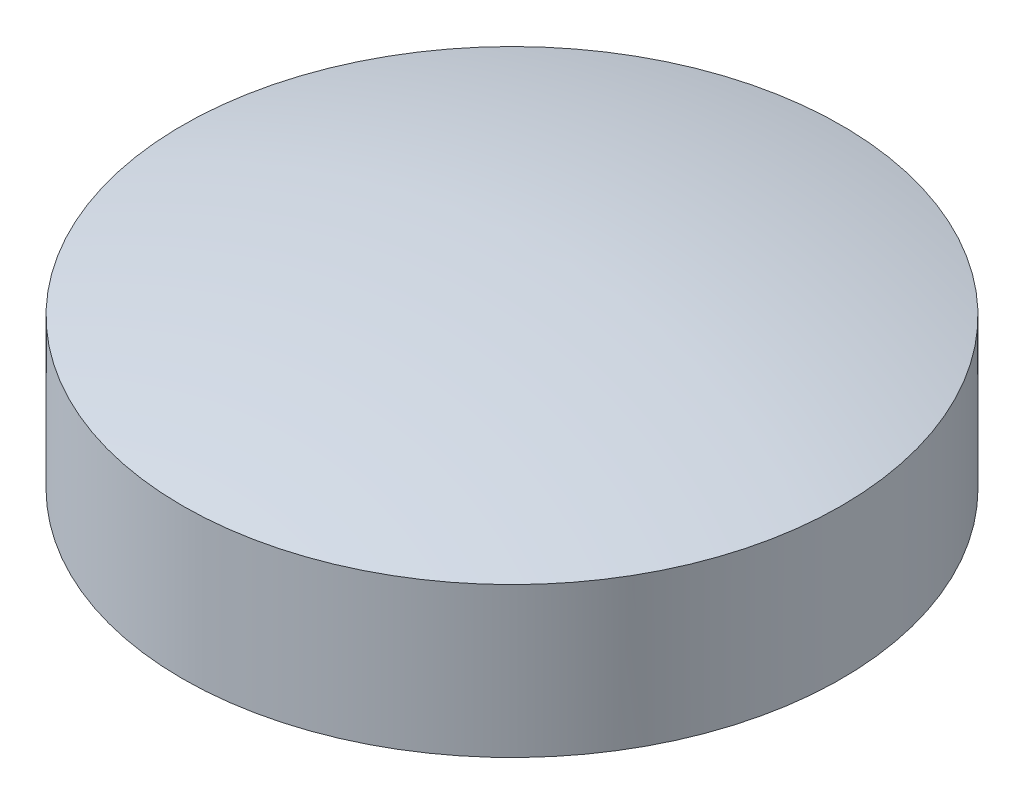
SolidWorks part; units mm, degrees
ref_plane "Front Plane" through (0, 0, 0) normal (0, 0, 1) x (1, 0, 0)
ref_plane "Top Plane" through (0, 0, 0) normal (0, 1, 0) x (1, 0, 0)
ref_plane "Right Plane" through (0, 0, 0) normal (1, 0, 0) x (0, 0, -1)
sketch "Sketch1" plane through (0, 0, 0) normal (0, 0, 1) x (1, 0, 0)
  line L0 (22, 0) -> (0, 0)
  line L1 (0, 0) -> (0, 10)
  line L2 (22, 0) -> (22, 13)
  line L3 (22, 29.7064) -> (22, -22.4626) construction
  arc A0 (22, 13) -> (0, 10) centre (22, -69.1667) ccw
  dimension "D1" = 22
  dimension "D2" = 13
  dimension "D3" = 10
revolve "Revolve1" add sketch "Sketch1" angle 360 about L3
sketch "Sketch2" plane through (0, 0, 0) normal (0, -1, 0) x (1, 0, 0)
  circle A0 centre (0, 0) radius 1.5
  dimension "D1" = 3
extrude "Cut-Extrude1" cut sketch "Sketch2" against normal blind 5
